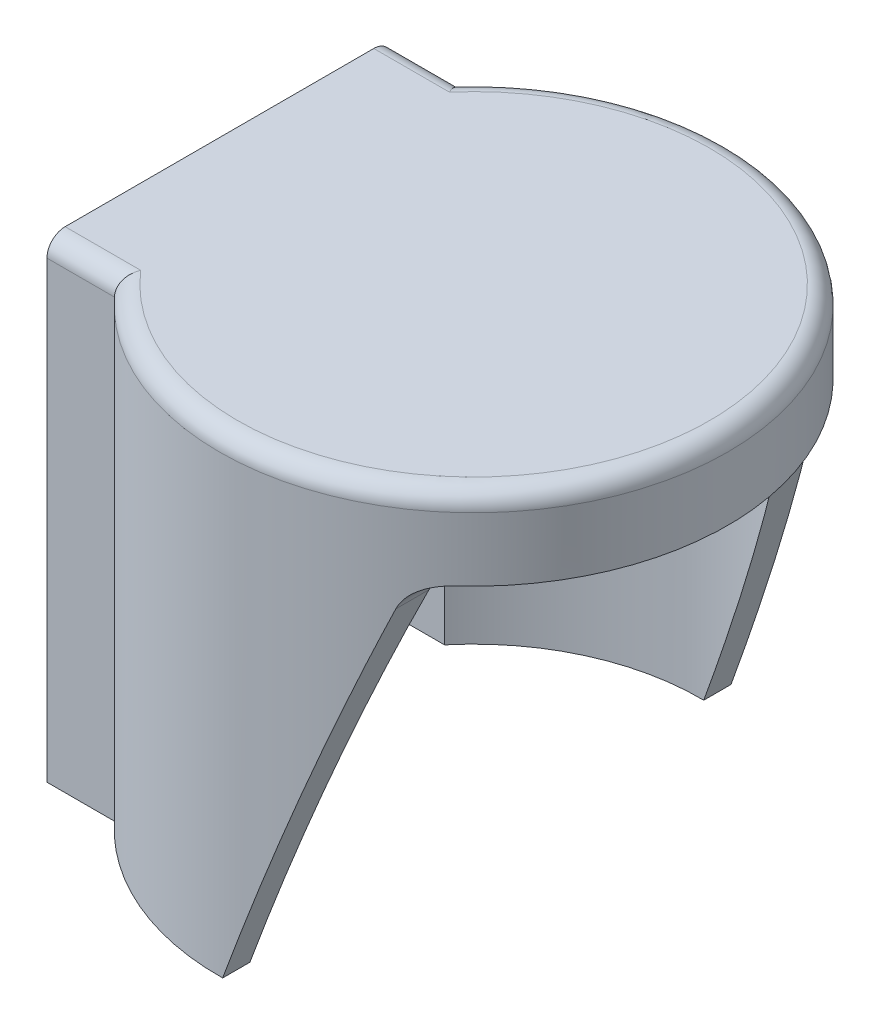
SolidWorks part; units mm, degrees
ref_plane "Front Plane" through (0, 0, 0) normal (0, 0, 1) x (1, 0, 0)
ref_plane "Top Plane" through (0, 0, 0) normal (0, 1, 0) x (1, 0, 0)
ref_plane "Right Plane" through (0, 0, 0) normal (1, 0, 0) x (0, 0, -1)
sketch "Sketch1" plane through (0, 0, 0) normal (0, 1, 0) x (1, 0, 0)
  circle A0 centre (0, 0) radius 14
  dimension "D1" = 28
extrude "Boss-Extrude1" add sketch "Sketch1" along normal blind 26
sketch "Sketch3" plane through (0, 0, 0) normal (0, 0, 1) x (1, 0, 0)
  line L0 (14, 26) -> (-14, 26) construction
  line L1 (0, 0) -> (-14, 0)
  line L2 (0, 0) -> (0, 26)
  line L3 (0, 26) -> (-14, 26)
  line L4 (-14, 0) -> (-14, 26)
  line L5 (14, 0) -> (14, 26) construction
  dimension "D1" = 28
extrude "Boss-Extrude2" add sketch "Sketch3" along normal mid plane 19
shell "Shell1" thickness 1.5
sketch "Sketch4" plane through (0, 0, 0) normal (0, 0, 1) x (1, 0, 0)
  line L0 (0.1746, 0) -> (7.521, 20.184)
  line L1 (-10.2835, 0) -> (14, 0) construction
  line L2 (9.4004, 21.5) -> (14, 21.5)
  line L3 (14, 0) -> (14, 26) construction
  line L4 (14, 26) -> (-10.2835, 26) construction
  line L5 (14, 21.5) -> (14, 0)
  line L6 (14, 0) -> (0.1746, 0)
  arc A0 (9.4004, 21.5) -> (7.521, 20.184) centre (9.4004, 19.5) ccw
  point P11 (8, 21.5)
  dimension "D4" = 2
  dimension "D1" = 4.5
  dimension "D2" = 6
  dimension "D3" = 110
extrude "Cut-Extrude1" cut sketch "Sketch4" against normal through all both and the other way through all
fillet "Fillet1" radius 1 3 edges at (-12.1417, 26, -9.5) (-12.1417, 26, 9.5) (14, 26, 0)
